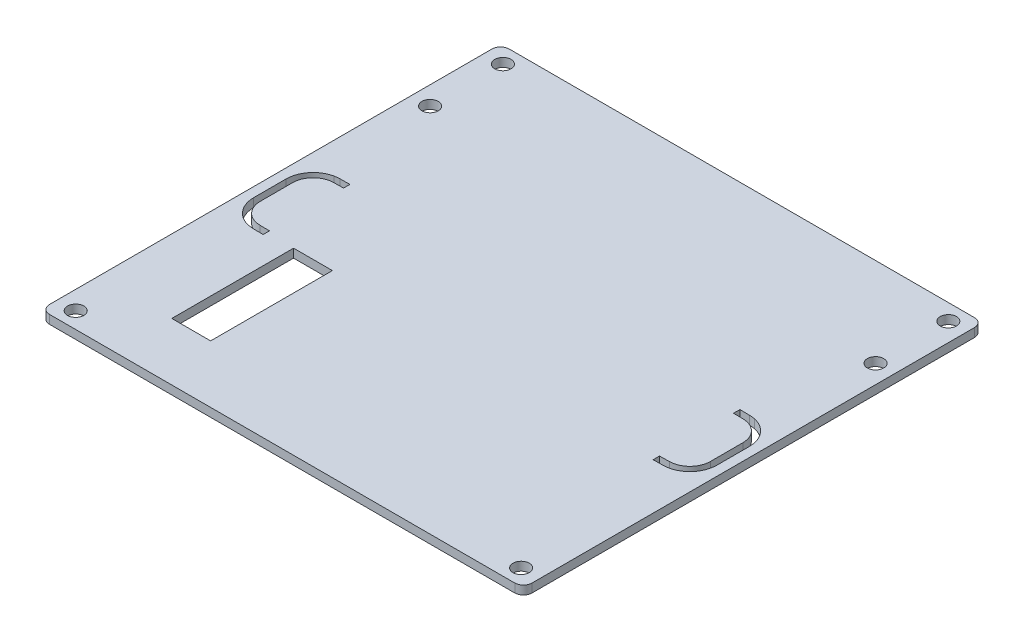
SolidWorks part; units mm, degrees
ref_plane "Front Plane" through (0, 0, 0) normal (0, 0, 1) x (1, 0, 0)
ref_plane "Top Plane" through (0, 0, 0) normal (0, 1, 0) x (1, 0, 0)
ref_plane "Right Plane" through (0, 0, 0) normal (1, 0, 0) x (0, 0, -1)
sketch "Sketch1" plane through (0, 0, 0) normal (0, 1, 0) x (1, 0, 0)
  line B0 (16.9607, 168.6299) -> (160.0393, 168.6299)
  line B1 (16.9607, 168.6299) -> (0, 168.6299)
  line B2 (0, 168.6299) -> (0, 0)
  line B3 (0, 0) -> (16.9607, 0)
  line B4 (16.9607, 0) -> (160.0393, 0)
  line B5 (160.0393, 0) -> (177, 0)
  line B6 (177, 0) -> (177, 168.6299)
  line B7 (177, 168.6299) -> (160.0393, 168.6299)
  line B8 (26.8753, 65.806) -> (41.1247, 65.806)
  line B9 (26.8753, 65.806) -> (26.8753, 21.1346)
  line B10 (26.8753, 21.1346) -> (41.1247, 21.1346)
  line B11 (41.1247, 65.806) -> (41.1247, 21.1346)
  line B12 (16.951, 64.5401) -> (16.9918, 66.8744)
  line B13 (16.9918, 66.8744) -> (13.3673, 66.9376)
  line B14 (5.8952, 74.5412) -> (5.8952, 86.3986)
  line B15 (13.3673, 94.0022) -> (16.9874, 94.0654)
  line B16 (16.9874, 94.0654) -> (16.9464, 96.4101)
  line B17 (16.9464, 96.4101) -> (13.3264, 96.3469)
  line B18 (11.4395, 96.1328) -> (11.3759, 96.1525)
  line B19 (3.5175, 86.3986) -> (3.5175, 74.5412)
  line B20 (11.3759, 64.7873) -> (11.4598, 64.8135)
  line B21 (13.3265, 64.6033) -> (16.951, 64.5401)
  line B22 (160.0125, 66.8788) -> (160.0534, 64.5401)
  line B23 (160.0534, 64.5401) -> (163.6735, 64.6033)
  line B24 (165.5403, 64.8135) -> (165.6241, 64.7873)
  line B25 (173.4825, 74.5412) -> (173.4825, 86.3986)
  line B26 (165.6241, 96.1525) -> (165.5605, 96.1328)
  line B27 (163.6736, 96.3469) -> (160.0491, 96.4102)
  line B28 (160.0491, 96.4102) -> (160.0081, 94.061)
  line B29 (160.0081, 94.061) -> (163.6326, 93.9978)
  line B30 (171.1004, 86.3986) -> (171.1004, 74.5412)
  line B31 (163.6326, 66.942) -> (160.0125, 66.8788)
  circle B32 centre (6.8007, 162.6692) radius 3
  circle B33 centre (6.8007, 135.9692) radius 3
  circle B34 centre (170.1993, 162.6692) radius 3
  circle B35 centre (170.1993, 135.9692) radius 3
  circle B36 centre (6.8007, 5.9649) radius 3
  circle B37 centre (170.1993, 5.9649) radius 3
  arc B38 (5.8952, 74.5412) -> (13.3673, 66.9376) centre (13.5, 74.5412) ccw
  arc B39 (13.3673, 94.0022) -> (5.8952, 86.3986) centre (13.5, 86.3986) ccw
  arc B40 (13.3264, 96.3469) -> (11.4395, 96.1328) centre (13.5, 86.3986) ccw
  arc B41 (11.3759, 96.1525) -> (3.5175, 86.3986) centre (13.5, 86.3986) ccw
  arc B42 (3.5175, 74.5412) -> (11.3759, 64.7873) centre (13.5, 74.5412) ccw
  arc B43 (11.4598, 64.8135) -> (13.3265, 64.6033) centre (13.5, 74.5412) ccw
  arc B44 (163.6735, 64.6033) -> (165.5403, 64.8135) centre (163.5, 74.5412) ccw
  arc B45 (165.6241, 64.7873) -> (173.4825, 74.5412) centre (163.5, 74.5412) ccw
  arc B46 (173.4825, 86.3986) -> (165.6241, 96.1525) centre (163.5, 86.3986) ccw
  arc B47 (165.5605, 96.1328) -> (163.6736, 96.3469) centre (163.5, 86.3986) ccw
  arc B48 (171.1004, 86.3986) -> (163.6326, 93.9978) centre (163.5, 86.3986) ccw
  arc B49 (163.6326, 66.942) -> (171.1004, 74.5412) centre (163.5, 74.5412) ccw
sketch_block_instance "Block-TopPlate-1"
sketch_block "Block-TopPlate" parameters "D1"=6, "D2"=10.16, "D3"=10.16, "D4"=3.175
extrude "Boss-Extrude1" add sketch "Sketch1" along normal blind 3.175
fillet "Fillet1" radius 3.175 4 edges at (0, 1.5875, -168.6299) (177, 1.5875, -168.6299) (177, 1.5875, 0) (0, 1.5875, 0)
